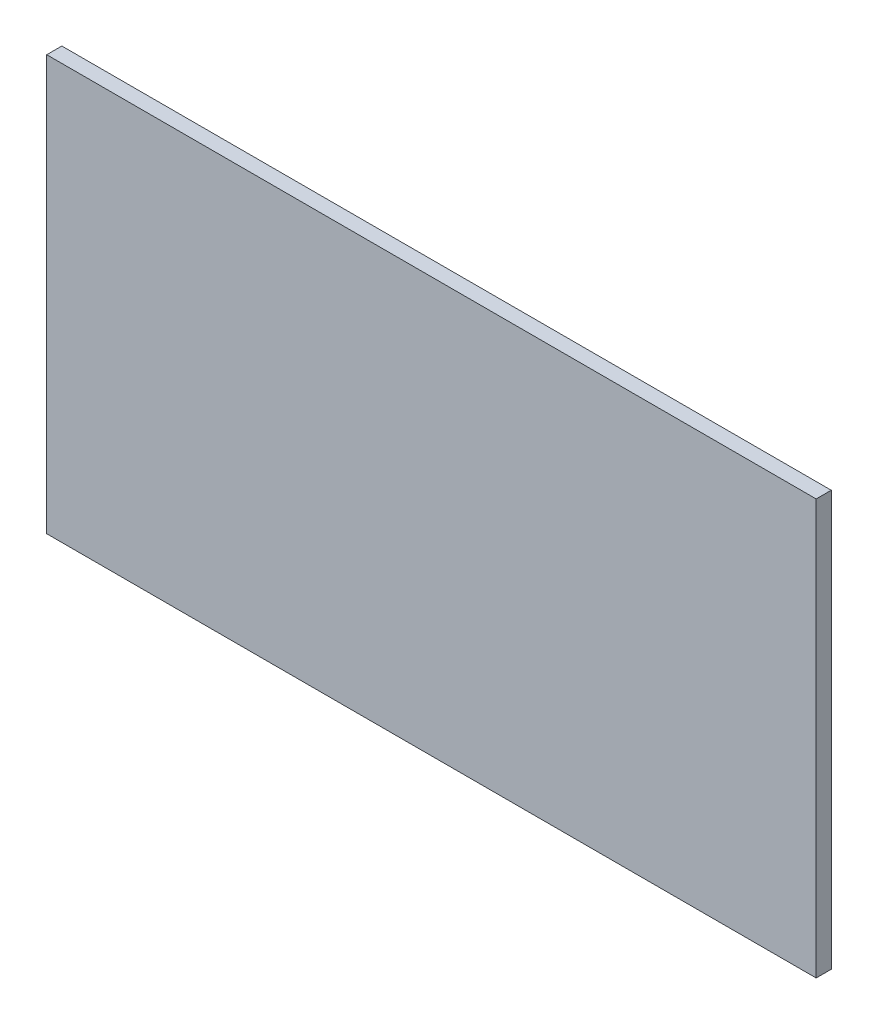
SolidWorks part; units mm, degrees
material "Cedar"
ref_plane "Front" through (0, 0, 0) normal (0, 0, 1) x (1, 0, 0)
ref_plane "Top" through (0, 0, 0) normal (0, 1, 0) x (1, 0, 0)
ref_plane "Right" through (0, 0, 0) normal (1, 0, 0) x (0, 0, -1)
sketch "Sketch1" plane through (0, 0, 0) normal (0, 0, 1) x (1, 0, 0)
  line L1 (-255, -137.5) -> (255, -137.5)
  line L2 (-255, -137.5) -> (-255, 137.5)
  line L3 (-255, 137.5) -> (255, 137.5)
  line L4 (255, -137.5) -> (255, 137.5)
  line L5 (-255, -137.5) -> (255, 137.5) construction
  line L6 (-255, 137.5) -> (255, -137.5) construction
  point P0 (0, 0)
  dimension "D1" = 275
  dimension "D2" = 510
extrude "Boss-Extrude1" add sketch "Sketch1" along normal blind 10
